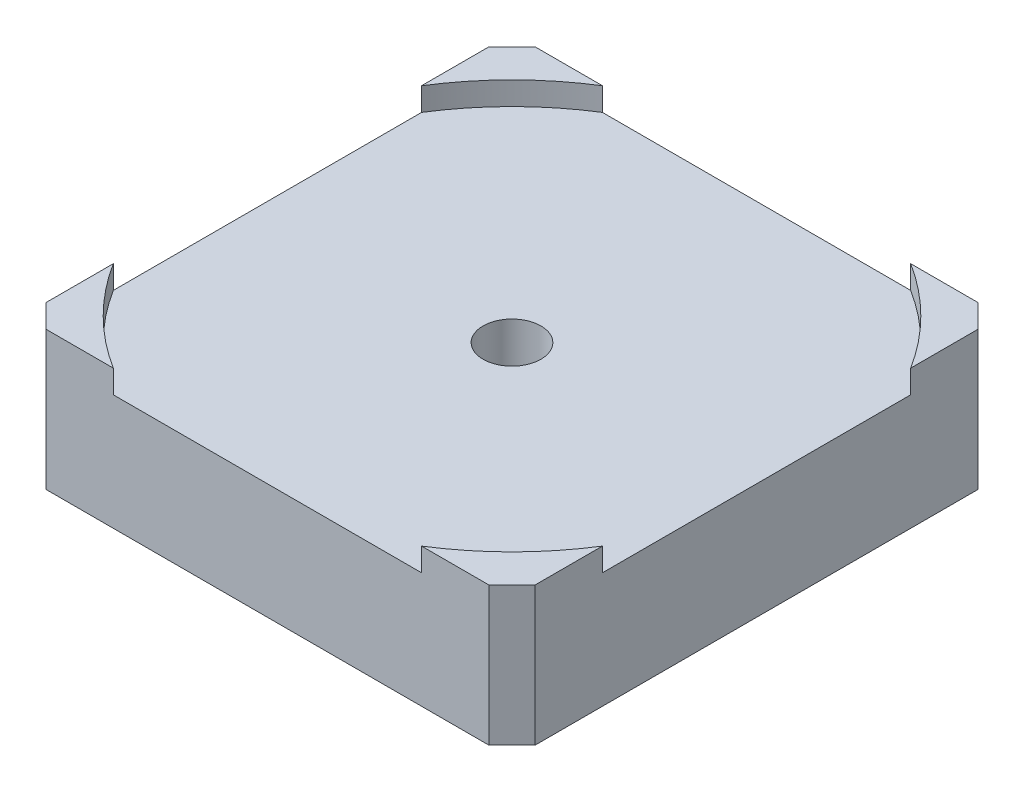
SolidWorks part; units mm, degrees
ref_plane "Alzado" through (0, 0, 0) normal (0, 0, 1) x (1, 0, 0)
ref_plane "Planta" through (0, 0, 0) normal (0, 1, 0) x (1, 0, 0)
ref_plane "Vista lateral" through (0, 0, 0) normal (1, 0, 0) x (0, 0, -1)
sketch "Croquis1" plane through (0, 0, 0) normal (0, 1, 0) x (1, 0, 0)
  line L1 (-21.15, -21.15) -> (21.15, -21.15)
  line L2 (-21.15, -21.15) -> (-21.15, 21.15)
  line L3 (-21.15, 21.15) -> (21.15, 21.15)
  line L4 (21.15, -21.15) -> (21.15, 21.15)
  line L5 (-21.15, -21.15) -> (21.15, 21.15) construction
  line L6 (-21.15, 21.15) -> (21.15, -21.15) construction
  point P0 (0, 0)
  dimension "D1" = 42.3
  dimension "D2" = 42.3
extrude "Saliente-Extruir1" add sketch "Croquis1" along normal blind 12
sketch "Croquis2" plane through (0, 12, 0) normal (0, 1, 0) x (1, 0, 0)
  line L0 (-21.15, 13.3296) -> (-21.15, -13.3296)
  line L2 (-13.3296, -21.15) -> (13.3296, -21.15)
  line L3 (-13.3296, 21.15) -> (13.3296, 21.15)
  line L4 (21.15, 13.3296) -> (21.15, -13.3296)
  line L5 (21.15, 21.15) -> (-21.15, 21.15) construction
  line L6 (-21.15, 21.15) -> (-21.15, -21.15) construction
  line L7 (-21.15, -21.15) -> (21.15, -21.15) construction
  line L9 (21.15, -21.15) -> (21.15, 21.15) construction
  arc A0 (-21.15, -13.3296) -> (-13.3296, -21.15) centre (0, 0) ccw
  arc A1 (-13.3296, 21.15) -> (-21.15, 13.3296) centre (0, 0) ccw
  arc A2 (21.15, 13.3296) -> (13.3296, 21.15) centre (0, 0) ccw
  arc A3 (13.3296, -21.15) -> (21.15, -13.3296) centre (0, 0) ccw
  dimension "D1" = 50
extrude "Cortar-Extruir1" cut sketch "Croquis2" against normal blind 2
chamfer "Chaflán1" distance 2 angle 45 4 edges at (21.15, 6, -21.15) (-21.15, 6, -21.15) (-21.15, 6, 21.15) (21.15, 6, 21.15)
sketch "Croquis3" plane through (0, 10, 0) normal (0, 1, 0) x (1, 0, 0)
  circle A0 centre (0, 0) radius 2.5
  dimension "D1" = 5
extrude "Cortar-Extruir2" cut sketch "Croquis3" against normal through all
